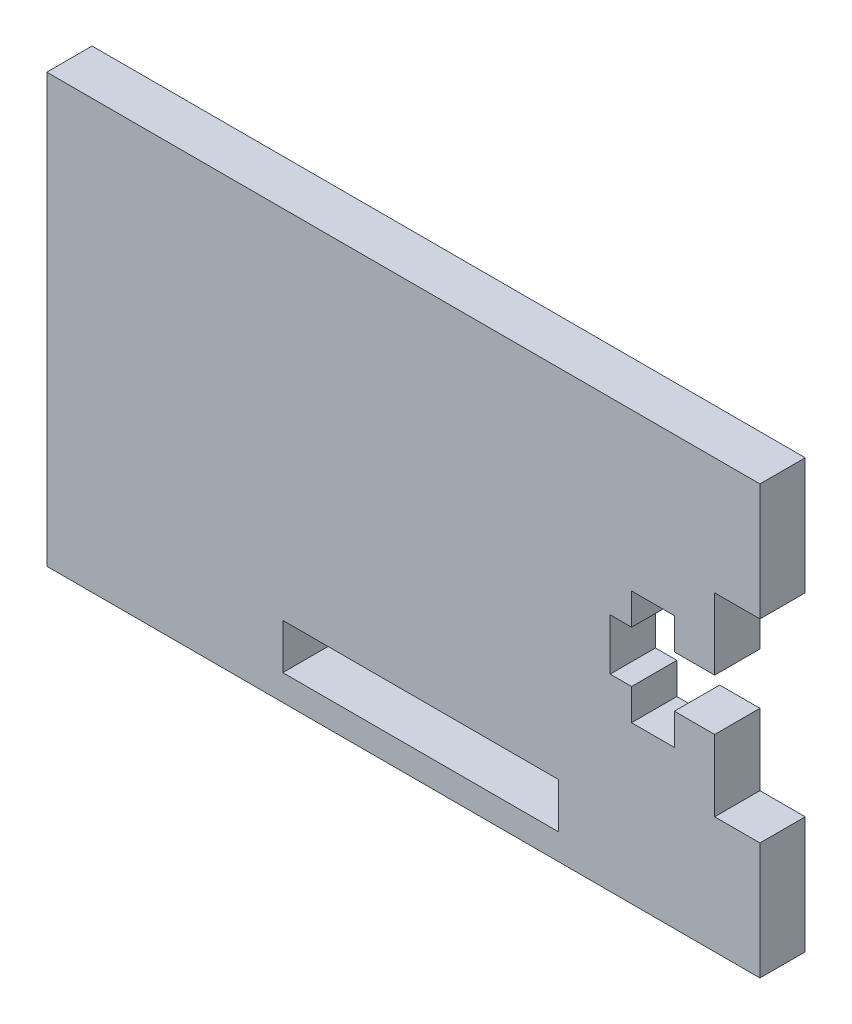
SolidWorks part; units mm, degrees
ref_plane "정면" through (0, 0, 0) normal (0, 0, 1) x (1, 0, 0)
ref_plane "윗면" through (0, 0, 0) normal (0, 1, 0) x (1, 0, 0)
ref_plane "우측면" through (0, 0, 0) normal (1, 0, 0) x (0, 0, -1)
sketch "Sketch1" plane through (0, 0, 0) normal (0, 0, 1) x (1, 0, 0)
  line L1 (-96.9113, 47.7808) -> (-46.9113, 47.7808)
  line L2 (-96.9113, 47.7808) -> (-96.9113, 17.7808)
  line L3 (-96.9113, 17.7808) -> (-46.9113, 17.7808)
  line L4 (-46.9113, 47.7808) -> (-46.9113, 39.5808)
  line L6 (-46.9113, 39.5808) -> (-50.0863, 39.5808)
  line L7 (-50.0863, 39.5808) -> (-50.0863, 34.5808)
  line L8 (-50.0863, 34.5808) -> (-52.9113, 34.5808)
  line L9 (-52.9113, 34.5808) -> (-52.9113, 36.7808)
  line L10 (-52.9113, 36.7808) -> (-55.9113, 36.7808)
  line L11 (-55.9113, 36.7808) -> (-55.9113, 34.5808)
  line L12 (-55.9113, 34.5808) -> (-57.4113, 34.5808)
  line L13 (-57.4113, 34.5808) -> (-57.4113, 30.9808)
  line L14 (-55.9113, 30.9808) -> (-57.4113, 30.9808)
  line L15 (-55.9113, 28.7808) -> (-55.9113, 30.9808)
  line L16 (-52.9113, 28.7808) -> (-55.9113, 28.7808)
  line L17 (-52.9113, 30.9808) -> (-52.9113, 28.7808)
  line L18 (-50.0863, 30.9808) -> (-52.9113, 30.9808)
  line L19 (-50.0863, 25.9808) -> (-50.0863, 30.9808)
  line L20 (-46.9113, 25.9808) -> (-50.0863, 25.9808)
  line L21 (-46.9113, 25.9808) -> (-46.9113, 17.7808)
  line L37 (-61.0251, 19.5952) -> (-80.3636, 19.5952)
  line L38 (-61.0251, 19.5952) -> (-61.0251, 22.7702)
  line L39 (-61.0251, 22.7702) -> (-80.3636, 22.7702)
  line L40 (-80.3636, 19.5952) -> (-80.3636, 22.7702)
  point P16 (-57.4113, 32.7808)
extrude "Boss-Extrude1" add sketch "Sketch1" along normal blind 3.175
